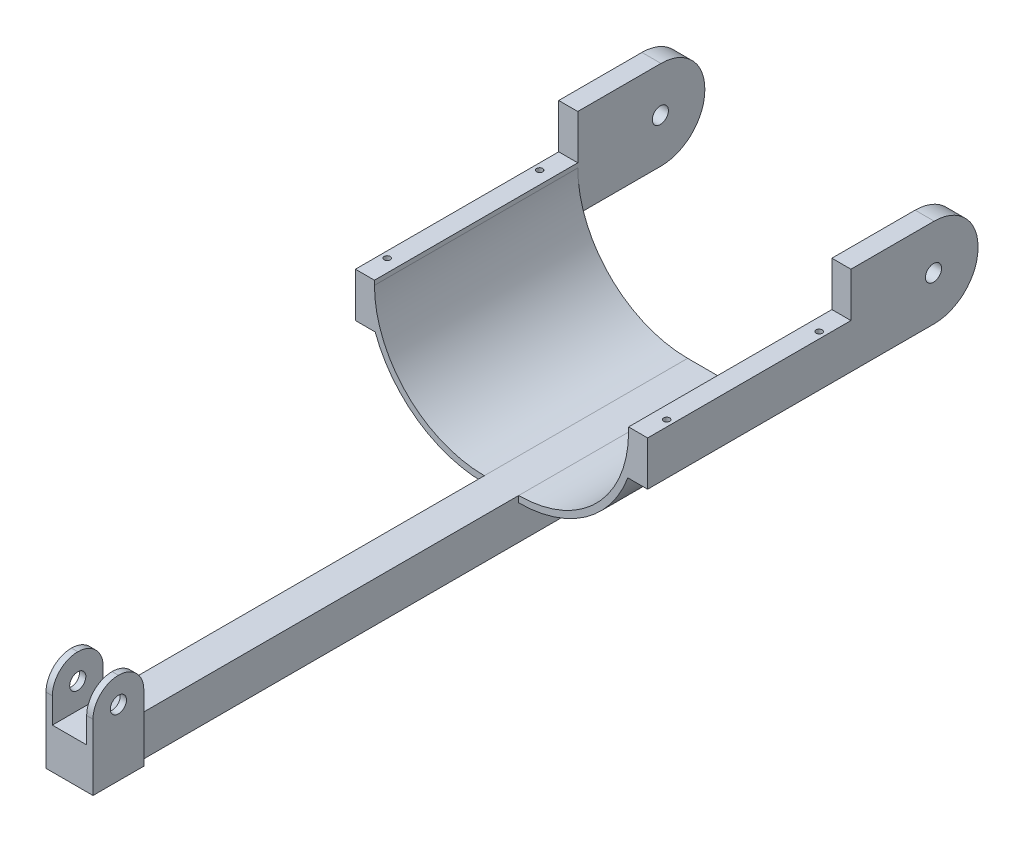
SolidWorks part; units mm, degrees
ref_plane "Front Plane" through (0, 0, 0) normal (0, 0, 1) x (1, 0, 0)
ref_plane "Top Plane" through (0, 0, 0) normal (0, 1, 0) x (1, 0, 0)
ref_plane "Right Plane" through (0, 0, 0) normal (1, 0, 0) x (0, 0, -1)
sketch "Sketch1" plane through (0, 0, 0) normal (0, 0, 1) x (1, 0, 0)
  line L1 (86.5, 0) -> (113.5, 0)
  line L2 (0, 86.5) -> (0, 90)
  line L4 (200, 86.5) -> (200, 90)
  line L5 (205, 86.5) -> (205, 90)
  line L6 (86.5, -5) -> (113.5, -5)
  line L7 (-5, 86.5) -> (-5, 90)
  line L8 (-5, 90) -> (205, 90)
  line L9 (-5, 90) -> (-5, 87.5488)
  line L10 (-5, 85) -> (-4.9791, 85)
  line L11 (-5, 90) -> (-15, 90)
  line L12 (-5, 90) -> (-5, 86.5)
  line L13 (-5, 85) -> (-15, 85)
  line L14 (-15, 90) -> (-15, 85)
  line L15 (205, 85) -> (204.9608, 85)
  line L16 (205, 90) -> (215, 90)
  line L17 (205, 90) -> (205, 86.5)
  line L18 (205, 85) -> (215, 85)
  line L19 (215, 90) -> (215, 85)
  arc A0 (113.5, 0) -> (200, 86.5) centre (113.5, 86.5) ccw
  arc A1 (86.5, 0) -> (0, 86.5) centre (86.5, 86.5) cw
  arc A2 (113.5, -5) -> (205, 86.5) centre (113.5, 86.5) ccw
  arc A3 (86.5, -5) -> (-5, 86.5) centre (86.5, 86.5) cw
  point P10 (200, 0)
  point P13 (0, 0)
  dimension "D4" = 86.5
  dimension "D1" = 5
  dimension "D2" = 10
  dimension "D3" = 5
  dimension "D5" = 10
extrude "Boss-Extrude1" add sketch "Sketch1" along normal blind 160
sketch "Sketch2" plane through (0, 85, 0) normal (0, -1, 0) x (1, 0, 0)
  line L0 (-9.9939, 0) -> (-9.9939, 160)
  line L1 (-15, 0) -> (-4.9877, 0) construction
  line L2 (-15, 160) -> (-4.9877, 160) construction
  line L3 (209.9939, 160) -> (209.9939, 0)
  line L4 (215, 160) -> (204.9877, 160) construction
  line L5 (215, 0) -> (204.9877, 0) construction
  circle A0 centre (-9.9939, 20) radius 2.3813
  circle A1 centre (-9.9939, 140) radius 2.3813
  circle A2 centre (209.9939, 140) radius 2.3813
  circle A3 centre (209.9939, 20) radius 2.3813
  dimension "D1" = 4.7625
  dimension "D2" = 4.7625
  dimension "D3" = 4.7625
  dimension "D4" = 4.7625
  dimension "D5" = 20
  dimension "D6" = 20
  dimension "D7" = 20
  dimension "D8" = 20
extrude "Cut-Extrude1" cut sketch "Sketch2" against normal blind 160 contours L0 A1 | L0 A1 | A0 | A3 | A2
sketch "Sketch3" plane through (0, -5, 0) normal (0, -1, 0) x (-1, 0, 0)
  line L1 (-86.5, 0) -> (-113.5, 0)
  line L2 (-86.5, 0) -> (-86.5, -500)
  line L3 (-86.5, -500) -> (-113.5, -500)
  line L4 (-113.5, 0) -> (-113.5, -500)
  dimension "D1" = 500
extrude "Boss-Extrude2" add sketch "Sketch3" along normal blind 27
sketch "Sketch4" plane through (0, -5, 0) normal (0, 1, 0) x (1, 0, 0)
  line L4 (113.5, -500) -> (113.5, -160)
  line L5 (113.5, -160) -> (86.5, -160)
  line L6 (86.5, -160) -> (86.5, -500)
  line L7 (86.5, -500) -> (113.5, -500)
  line L8 (113.5, -500) -> (113.5, -160)
  line L9 (113.5, -160) -> (86.5, -160)
  line L10 (86.5, -160) -> (86.5, -500)
  line L11 (86.5, -500) -> (113.5, -500)
  dimension "D1" = 0
extrude "Boss-Extrude3" add sketch "Sketch4" along normal blind 5
sketch "Sketch5" plane through (113.5, 0, 0) normal (1, 0, 0) x (0, 0, -1)
  line L0 (-500, 0) -> (-160, 0) construction
  line L1 (-500, -32) -> (-460, -32)
  line L2 (-500, -32) -> (-500, 20.01)
  line L3 (-480.01, 40) -> (-479.99, 40)
  line L4 (-460, -32) -> (-460, 20.01)
  line L5 (-460, 40) -> (-500, 0)
  line L6 (-460, 40) -> (-500, 40)
  line L7 (-460, 40) -> (-460, 0)
  line L8 (-460, 0) -> (-500, 0)
  line L9 (-500, 40) -> (-500, 0)
  circle A0 centre (-480, 20) radius 6.35
  arc A1 (-479.99, 40) -> (-460, 20.01) centre (-479.99, 20.01) cw
  arc A2 (-500, 20.01) -> (-480.01, 40) centre (-480.01, 20.01) cw
  line M11 (-160, 0) -> (-500, 0)
  line M12 (-500, 0) -> (-500, -32)
  line M13 (-500, -32) -> (0, -32)
  dimension "D3" = 12.7
  dimension "D4" = 19.99
  dimension "D1" = 40
  dimension "D2" = 40
extrude "Boss-Extrude4" add sketch "Sketch5" along normal blind 5 contours A2 L2 L5 A0 A1 L3 | A1 L5 A0 L4 M11 | L4 M13 M11 M12
sketch "Sketch6" plane through (86.5, 0, 0) normal (-1, 0, 0) x (0, 0, 1)
  line L4 (460, 0) -> (500, 0)
  line L5 (500, 0) -> (500, 20.01)
  line L6 (480.01, 40) -> (479.99, 40)
  line L7 (460, 20.01) -> (460, 0)
  line L8 (460, 0) -> (500, 0)
  line L9 (500, 0) -> (500, 20.01)
  line L10 (480.01, 40) -> (479.99, 40)
  line L11 (460, 20.01) -> (460, 0)
  line L12 (500, -32) -> (500, 20.01)
  line L13 (460, -32) -> (500, -32)
  line L14 (460, 20.01) -> (460, -32)
  line L15 (480.01, 40) -> (479.99, 40)
  line L16 (500, -32) -> (500, 20.01)
  line L17 (460, -32) -> (500, -32)
  line L18 (460, 20.01) -> (460, -32)
  line L19 (480.01, 40) -> (479.99, 40)
  circle A0 centre (480, 20) radius 6.35 construction
  circle A1 centre (480, 20) radius 6.35
  arc A2 (500, 20.01) -> (480.01, 40) centre (480.01, 20.01) ccw
  arc A3 (479.99, 40) -> (460, 20.01) centre (479.99, 20.01) ccw
  arc A4 (500, 20.01) -> (480.01, 40) centre (480.01, 20.01) ccw
  arc A5 (479.99, 40) -> (460, 20.01) centre (479.99, 20.01) ccw
  arc A8 (479.99, 40) -> (460, 20.01) centre (479.99, 20.01) ccw
  arc A9 (500, 20.01) -> (480.01, 40) centre (480.01, 20.01) ccw
  arc A10 (479.99, 40) -> (460, 20.01) centre (479.99, 20.01) ccw
  arc A11 (500, 20.01) -> (480.01, 40) centre (480.01, 20.01) ccw
  line M14 (500, -32) -> (500, 0)
  line M15 (500, 0) -> (160, 0)
  line M19 (0, -32) -> (500, -32)
  dimension "D1" = 0
  dimension "D2" = 0
extrude "Boss-Extrude5" add sketch "Sketch6" along normal blind 5 contours L18 M15 M19 M14 | L10 A5 L11 L9 A4 A1 M15
sketch "Sketch7" plane through (0, 0, 0) normal (0, 0, -1) x (-1, 0, 0)
  line L1 (-204.9877, 85) -> (-215, 85)
  line L2 (-204.9877, 85) -> (-204.9877, 95)
  line L3 (-204.9877, 95) -> (-215, 95)
  line L4 (-215, 85) -> (-215, 95)
  line L5 (-215, 95) -> (-204.9877, 95)
  line L6 (-215, 95) -> (-215, 125)
  line L7 (-215, 125) -> (-204.9877, 125)
  line L8 (-204.9877, 95) -> (-204.9877, 125)
  line L9 (-215, 85) -> (-204.9877, 85)
  line L10 (-215, 85) -> (-215, 55)
  line L11 (-215, 55) -> (-204.9877, 55)
  line L12 (-204.9877, 85) -> (-204.9877, 55)
  line M13 (-200, 90) -> (-215, 90)
  line M14 (-215, 90) -> (-215, 85)
  line M15 (-215, 85) -> (-204.9877, 85)
  dimension "D1" = 10
  dimension "D2" = 30
  dimension "D3" = 30
extrude "Boss-Extrude6" add sketch "Sketch7" along normal blind 100 contours L12 L10 L11 M15 | L4 L2 L3 M13 | L2 M15 M13 M14 | L3 L8 L7 L6
sketch "Sketch8" plane through (0, 0, 160) normal (0, 0, 1) x (1, 0, 0)
  line L0 (215, 55) -> (199.4069, 55)
  line L4 (215, 55) -> (215, 85)
  line L5 (113.5, 0) -> (113.5, -5)
  line L6 (204.9877, 85) -> (215, 85)
  line L7 (215, 85) -> (215, 90)
  line L8 (215, 90) -> (200, 90)
  line L9 (200, 90) -> (200, 86.5)
  line L10 (113.5, 0) -> (113.5, -5)
  line L11 (204.9877, 85) -> (215, 85)
  line L12 (215, 85) -> (215, 90)
  line L13 (215, 90) -> (200, 90)
  line L14 (200, 90) -> (200, 86.5)
  line L15 (215, 85) -> (204.9877, 85)
  line L16 (204.9877, 85) -> (204.9877, 55)
  line L17 (204.9877, 55) -> (215, 55)
  line L18 (215, 55) -> (215, 85)
  line L19 (215, 85) -> (204.9877, 85)
  line L20 (204.9877, 85) -> (204.9877, 55)
  line L21 (204.9877, 55) -> (215, 55)
  arc A2 (113.5, 0) -> (200, 86.5) centre (113.5, 86.5) ccw
  arc A3 (113.5, -5) -> (204.9877, 85) centre (113.5, 86.5) ccw
  arc A4 (113.5, 0) -> (200, 86.5) centre (113.5, 86.5) ccw
  arc A5 (113.5, -5) -> (204.9877, 85) centre (113.5, 86.5) ccw
  arc M14 (113.5, -5) -> (204.9877, 85) centre (113.5, 86.5) ccw
  line M15 (204.9877, 85) -> (215, 85)
  dimension "D1" = 0
  dimension "D2" = 0
extrude "Boss-Extrude7" add sketch "Sketch8" against normal up to vertex contours L20 L0 M14 | L20 L0 L18 M15
sketch "Sketch9" plane through (215, 0, 0) normal (1, 0, 0) x (0, 0, -1)
  line L0 (100, 55) -> (-160, 55) construction
  line L1 (65.5, 125) -> (30, 125)
  line L2 (100, 90.5) -> (100, 89.5)
  line L3 (65.5, 55) -> (30, 55)
  line L4 (30, 125) -> (30, 55)
  line L5 (30, 125) -> (100, 55)
  circle A0 centre (65, 90) radius 6.35
  arc A1 (100, 89.5) -> (65.5, 55) centre (65.5, 89.5) cw
  arc A2 (65.5, 125) -> (100, 90.5) centre (65.5, 90.5) cw
  point P14 (100, 125)
  line M8 (-160, 55) -> (100, 55)
  line M9 (100, 55) -> (100, 125)
  line M10 (100, 125) -> (0, 125)
  dimension "D2" = 12.7
  dimension "D3" = 34.5
  dimension "D1" = 70
extrude "Cut-Extrude2" cut sketch "Sketch9" against normal blind 100 contours L5 A0 | L5 A0 | L5 A1 M8 | A1 L5 M9 | A2 M10 M9
sketch "Sketch10" plane through (-15, 0, 0) normal (-1, 0, 0) x (0, 0, 1)
  line L4 (0, 90) -> (0, 85)
  line L5 (0, 85) -> (160, 85)
  line L6 (160, 85) -> (160, 90)
  line L7 (160, 90) -> (0, 90)
  line L8 (0, 90) -> (0, 85)
  line L9 (0, 85) -> (160, 85)
  line L10 (160, 85) -> (160, 90)
  line L11 (160, 90) -> (0, 90)
  line L13 (-100, 90.5) -> (-100, 89.5)
  line L14 (-65.5, 55) -> (0, 55)
  line L15 (0, 55) -> (0, 90)
  line L16 (0, 90) -> (0, 125)
  line L17 (0, 125) -> (-65.5, 125)
  line L18 (-100, 90.5) -> (-100, 89.5)
  line L19 (-65.5, 55) -> (0, 55)
  line L20 (0, 55) -> (0, 90)
  line L21 (0, 90) -> (0, 125)
  line L22 (0, 125) -> (-65.5, 125)
  circle A0 centre (-65, 90) radius 6.35 construction
  circle A1 centre (-65, 90) radius 6.35
  arc A2 (-65.5, 125) -> (-100, 90.5) centre (-65.5, 90.5) ccw
  arc A3 (-100, 89.5) -> (-65.5, 55) centre (-65.5, 89.5) ccw
  arc A4 (-65.5, 125) -> (-100, 90.5) centre (-65.5, 90.5) ccw
  arc A5 (-100, 89.5) -> (-65.5, 55) centre (-65.5, 89.5) ccw
  line M12 (0, 90) -> (0, 85)
  dimension "D1" = 0
  dimension "D2" = 0
extrude "Boss-Extrude8" add sketch "Sketch10" against normal up to vertex (10.0123 mm away) contours L18 A5 L19 L20 L21 L22 A4 A1 M12
sketch "Sketch11" plane through (0, 0, 160) normal (0, 0, 1) x (1, 0, 0)
  line L0 (-15, 55) -> (5.9395, 55)
  line L4 (-4.9877, 85) -> (-15, 85)
  line L5 (-15, 85) -> (-15, 55)
  line L6 (-15, 55) -> (-4.9877, 55)
  line L7 (-4.9877, 55) -> (-4.9877, 85)
  line L8 (-4.9877, 85) -> (-15, 85)
  line L9 (-15, 85) -> (-15, 55)
  line L10 (-15, 55) -> (-4.9877, 55)
  line L11 (-4.9877, 55) -> (-4.9877, 85)
  arc A0 (0, 86.5) -> (86.5, 0) centre (86.5, 86.5) ccw construction
  arc M5 (-4.9877, 85) -> (86.5, -5) centre (86.5, 86.5) ccw
  line M11 (-15, 85) -> (-4.9877, 85)
  dimension "D1" = 0
extrude "Boss-Extrude9" add sketch "Sketch11" against normal up to vertex contours L0 L11 L9 M11 | L11 L0 M5
sketch "Sketch12" plane through (-4.9877, 0, 0) normal (1, 0, 0) x (0, 0, -1)
  line L5 (100, 89.5) -> (100, 90.5)
  line L6 (65.5, 125) -> (0, 125)
  line L7 (0, 125) -> (0, 90)
  line L8 (0, 90) -> (0, 55)
  line L9 (0, 55) -> (65.5, 55)
  line L10 (100, 89.5) -> (100, 90.5)
  line L11 (65.5, 125) -> (0, 125)
  line L12 (0, 125) -> (0, 90)
  line L13 (0, 90) -> (0, 55)
  line L14 (0, 55) -> (65.5, 55)
  circle A0 centre (65, 90) radius 6.35 construction
  circle A1 centre (65, 90) radius 6.35
  arc A2 (100, 90.5) -> (65.5, 125) centre (65.5, 90.5) ccw
  arc A3 (65.5, 55) -> (100, 89.5) centre (65.5, 89.5) ccw
  arc A4 (100, 90.5) -> (65.5, 125) centre (65.5, 90.5) ccw
  arc A5 (65.5, 55) -> (100, 89.5) centre (65.5, 89.5) ccw
  dimension "D1" = 0
extrude "Boss-Extrude10" add sketch "Sketch12" along normal up to vertex
sketch "Sketch13" plane through (204.9877, 0, 0) normal (-1, 0, 0) x (0, 0, 1)
  line L5 (-100, 90.5) -> (-100, 89.5)
  line L6 (-65.5, 55) -> (0, 55)
  line L7 (0, 55) -> (0, 90)
  line L8 (0, 90) -> (0, 125)
  line L9 (0, 125) -> (-65.5, 125)
  line L10 (-100, 90.5) -> (-100, 89.5)
  line L11 (-65.5, 55) -> (0, 55)
  line L12 (0, 55) -> (0, 90)
  line L13 (0, 90) -> (0, 125)
  line L14 (0, 125) -> (-65.5, 125)
  circle A0 centre (-65, 90) radius 6.35 construction
  circle A1 centre (-65, 90) radius 6.35
  arc A2 (-65.5, 125) -> (-100, 90.5) centre (-65.5, 90.5) ccw
  arc A3 (-100, 89.5) -> (-65.5, 55) centre (-65.5, 89.5) ccw
  arc A4 (-65.5, 125) -> (-100, 90.5) centre (-65.5, 90.5) ccw
  arc A5 (-100, 89.5) -> (-65.5, 55) centre (-65.5, 89.5) ccw
  dimension "D1" = 0
extrude "Boss-Extrude11" add sketch "Sketch13" along normal up to vertex
sketch "Sketch14" plane through (0, 85, 0) normal (0, 1, 0) x (1, 0, 0)
  circle A0 centre (-9.9939, -140) radius 2.3813 construction
  circle A1 centre (-9.9939, -20) radius 2.3813
  circle A2 centre (-9.9939, -20) radius 2.3813
  circle A3 centre (-9.9939, -140) radius 2.3813
  circle A4 centre (209.9939, -140) radius 2.3813 construction
  circle A5 centre (209.9939, -140) radius 2.3813
  circle A6 centre (209.9939, -20) radius 2.3813 construction
  circle A7 centre (209.9939, -20) radius 2.3813
  dimension "D1" = 0
extrude "Cut-Extrude3" cut sketch "Sketch14" against normal blind 200
